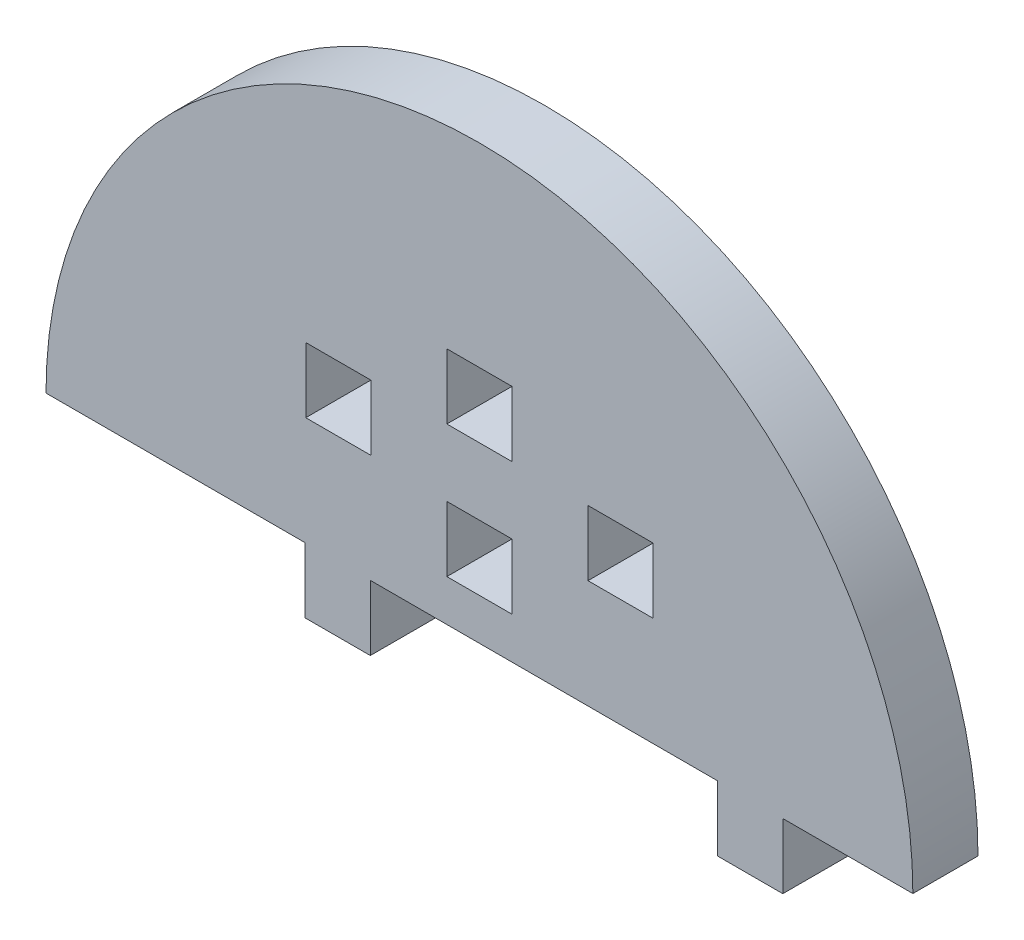
SolidWorks part; units mm, degrees
ref_plane "Front Plane" through (0, 0, 0) normal (0, 0, 1) x (1, 0, 0)
ref_plane "Top Plane" through (0, 0, 0) normal (0, 1, 0) x (1, 0, 0)
ref_plane "Right Plane" through (0, 0, 0) normal (1, 0, 0) x (0, 0, -1)
sketch "Model" plane through (0, 0, 0) normal (0, 0, 1) x (1, 0, 0)
  line L0 (3538.3357, 1077.7489) -> (3544.3357, 1077.7489)
  line L1 (3544.3357, 1077.7489) -> (3544.3357, 1071.7489)
  line L2 (3544.3357, 1071.7489) -> (3538.3357, 1071.7489)
  line L3 (3538.3357, 1071.7489) -> (3538.3357, 1077.7489)
  line L4 (3518.3357, 1077.7489) -> (3512.3357, 1077.7489)
  line L5 (3512.3357, 1077.7489) -> (3512.3357, 1071.7489)
  line L6 (3512.3357, 1071.7489) -> (3518.3357, 1071.7489)
  line L7 (3518.3357, 1071.7489) -> (3518.3357, 1077.7489)
  line L8 (3525.3357, 1083.7489) -> (3531.3357, 1083.7489)
  line L9 (3531.3357, 1083.7489) -> (3531.3357, 1077.7489)
  line L10 (3531.3357, 1077.7489) -> (3525.3357, 1077.7489)
  line L11 (3525.3357, 1077.7489) -> (3525.3357, 1083.7489)
  line L12 (3525.3357, 1065.5734) -> (3531.3357, 1065.5734)
  line L13 (3531.3357, 1065.5734) -> (3531.3357, 1071.5734)
  line L14 (3531.3357, 1071.5734) -> (3525.3357, 1071.5734)
  line L15 (3525.3357, 1071.5734) -> (3525.3357, 1065.5734)
  line L16 (3550.2843, 1061.7489) -> (3550.2843, 1055.7489)
  line L17 (3550.2843, 1055.7489) -> (3556.2843, 1055.7489)
  line L18 (3556.2843, 1055.7489) -> (3556.2843, 1061.7489)
  line L19 (3518.2843, 1061.7489) -> (3518.2843, 1055.7489)
  line L20 (3518.2843, 1055.7489) -> (3512.2843, 1055.7489)
  line L21 (3512.2843, 1055.7489) -> (3512.2843, 1061.7489)
  line L22 (3488.4071, 1061.7489) -> (3512.2843, 1061.7489)
  line L23 (3518.2843, 1061.7489) -> (3550.2843, 1061.7489)
  line L24 (3556.2843, 1061.7489) -> (3568.2643, 1061.7489)
  arc A0 (3568.2643, 1061.7489) -> (3488.4071, 1061.7489) centre (3528.3357, 1061.7489) ccw
extrude "Boss-Extrude1" add sketch "Model" along normal blind 6 contours L11 L10 L9 L8 | L14 L15 L12 L13 | L3 L2 L1 L0 | A0 L22 L21 L20 L19 L23 L16 L17 L18 L24 | L5 L6 L7 L4
